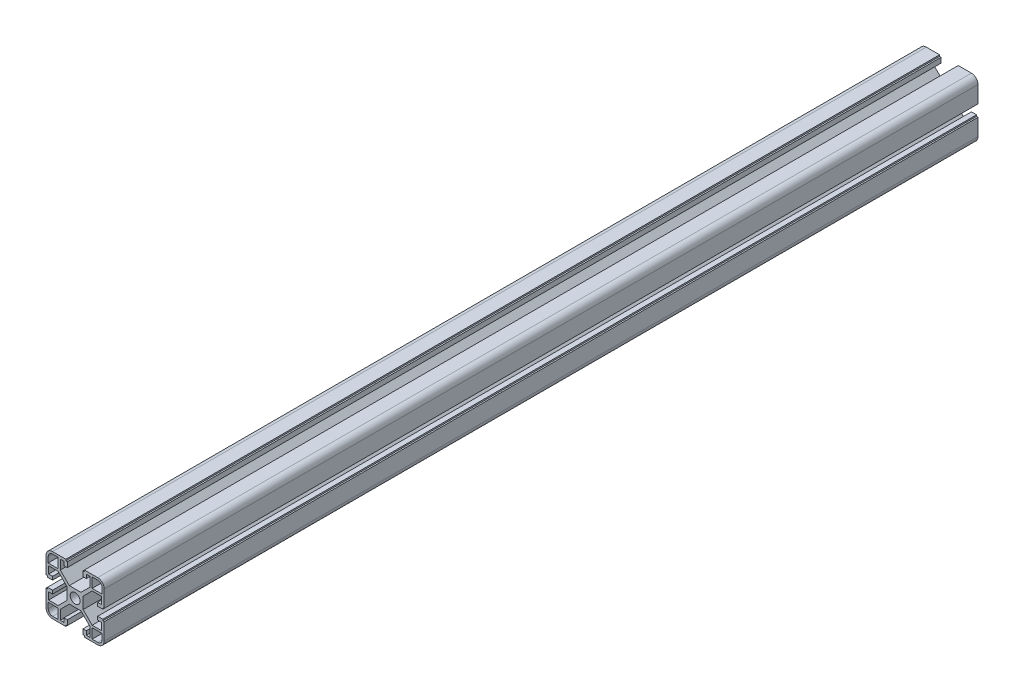
SolidWorks part; units mm, degrees
material "6061-T6 (SS)"
ref_plane "Front Plane" through (0, 0, 0) normal (0, 0, 1) x (1, 0, 0)
ref_plane "Top Plane" through (0, 0, 0) normal (0, 1, 0) x (1, 0, 0)
ref_plane "Right Plane" through (0, 0, 0) normal (1, 0, 0) x (0, 0, -1)
sketch "Sketch1" plane through (0, 0, 0) normal (0, 0, 1) x (1, 0, 0)
  line L0 (3.4, 0) -> (5.5, 0)
  line L1 (10.19, 11.69) -> (4, 5.5)
  line L2 (11.69, 10.19) -> (5.5, 4)
  line L3 (18.2, 10.19) -> (11.69, 10.19)
  line L4 (18.2, 10.19) -> (18.2, 5.2656)
  line L5 (18.2, 5.2656) -> (15.5, 5.2656)
  line L6 (15.5, 5.2656) -> (15.5, 2.9656)
  line L7 (15.5, 2.9656) -> (19, 2.9656)
  line L8 (19, 2.9656) -> (19, 3.9656)
  line L9 (19, 3.9656) -> (20, 3.9656)
  line L10 (20, 3.9656) -> (20, 15.5)
  line L11 (15.5, 20) -> (6.3853, 20)
  line L12 (18.5, 11.69) -> (18.5, 15.5)
  line L13 (15.5, 18.5) -> (11.69, 18.5)
  line L14 (11.69, 11.69) -> (11.69, 18.5)
  line L15 (0, 3.4) -> (0, 5.5)
  line L16 (4, 5.5) -> (0, 5.5)
  line L17 (6.3853, 20) -> (6.3853, 19)
  line L18 (5.5, 0) -> (5.5, 4)
  line L19 (6.3853, 19) -> (5.3853, 19)
  line L20 (5.3853, 19) -> (5.3853, 15.5)
  line L21 (5.3853, 15.5) -> (7.6853, 15.5)
  line L22 (10.19, 11.69) -> (10.19, 18.2)
  line L23 (11.69, 11.69) -> (18.5, 11.69)
  line L24 (7.6853, 18.2) -> (7.6853, 15.5)
  line L25 (10.19, 18.2) -> (7.6853, 18.2)
  arc A0 (20, 15.5) -> (15.5, 20) centre (15.5, 15.5) ccw
  arc A1 (18.5, 15.5) -> (15.5, 18.5) centre (15.5, 15.5) ccw
  arc A2 (3.4, 0) -> (0, 3.4) centre (0, 0) ccw
  dimension "D3" = 4.5
  dimension "D18" = 1.5
  dimension "D9" = 3.4
  dimension "D20" = 1.8
  dimension "D25" = 3
  dimension "D1" = 5.5
  dimension "D2" = 1.5
  dimension "D4" = 14.5
  dimension "D5" = 1.5
  dimension "D6" = 2.1
  dimension "D7" = 2.3
  dimension "D8" = 1.8
  dimension "D10" = 6.81
  dimension "D11" = 2.1
  dimension "D12" = 1
  dimension "D13" = 4.5
  dimension "D14" = 45
  dimension "D15" = 14.5
  dimension "D16" = 1
  dimension "D17" = 1.5
  dimension "D19" = 6.81
  dimension "D21" = 4.5
  dimension "D22" = 2.3
  dimension "D23" = 1
  dimension "D24" = 1
  dimension "D26" = 8.754
  dimension "D27" = 8.754
  dimension "D28" = 4.9244
  dimension "D29" = 2.5047
extrude "Boss-Extrude1" add sketch "Sketch1" along normal blind 600
mirror "Mirror1" about plane through (0, 0, 0) normal (0, 1, 0) of "Boss-Extrude1"
mirror "Mirror2" about plane through (0, 0, 0) normal (1, 0, 0) of "Boss-Extrude1"
mirror "Mirror3" about plane through (0, 0, 0) normal (0, 1, 0) of "Mirror2"
